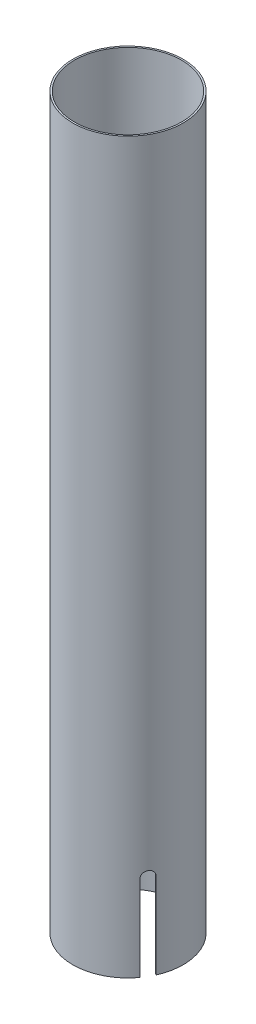
SolidWorks part; units mm, degrees
material "C-Glass Fiber"
ref_plane "Front Plane" through (0, 0, 0) normal (0, 0, 1) x (1, 0, 0)
ref_plane "Top Plane" through (0, 0, 0) normal (0, 1, 0) x (1, 0, 0)
ref_plane "Right Plane" through (0, 0, 0) normal (1, 0, 0) x (0, 0, -1)
sketch "Sketch1" plane through (0, 0, 0) normal (0, 1, 0) x (1, 0, 0)
  circle A0 centre (0, 0) radius 63.5
  circle A1 centre (0, 0) radius 65.4431
  dimension "D1" = 127
  dimension "D2" = 130.8862
extrude "Boss-Extrude1" add sketch "Sketch1" along normal blind 863.6
sketch "Sketch2" plane through (0, 0, 0) normal (0, 0, 1) x (1, 0, 0)
  line L0 (7, 0) -> (7, 101.6)
  line L1 (-65.4431, 0) -> (65.4431, 0) construction
  line L2 (7, 0) -> (-7, 0)
  line L3 (-7, 0) -> (-7, 101.6)
  arc A0 (7, 101.6) -> (-7, 101.6) centre (0, 101.6) ccw
  point P8 (0, 0)
  dimension "D1" = 7
  dimension "D2" = 101.6
extrude "Cut-Extrude1" cut sketch "Sketch2" against normal through all
pattern_circular "CirPattern1" count 3 over 360 about axis through (0, 0, 0) along (0, 1, 0) of "Cut-Extrude1"
